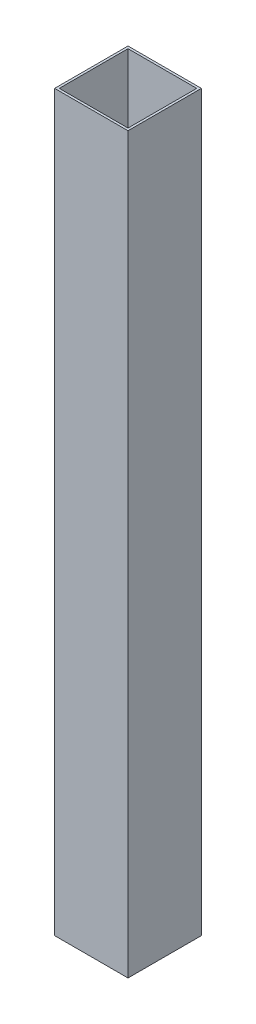
SolidWorks part; units mm, degrees
ref_plane "Front Plane" through (0, 0, 0) normal (0, 0, 1) x (1, 0, 0)
ref_plane "Top Plane" through (0, 0, 0) normal (0, 1, 0) x (1, 0, 0)
ref_plane "Right Plane" through (0, 0, 0) normal (1, 0, 0) x (0, 0, -1)
sketch "Sketch1" plane through (0, 0, 0) normal (0, 1, 0) x (1, 0, 0)
  line L1 (0, 0) -> (50.8, 0)
  line L2 (0, 0) -> (0, 50.8)
  line L3 (0, 50.8) -> (50.8, 50.8)
  line L4 (50.8, 0) -> (50.8, 50.8)
  line L5 (1.6002, 49.1998) -> (49.1998, 49.1998)
  line L6 (1.6002, 49.1998) -> (1.6002, 1.6002)
  line L7 (1.6002, 1.6002) -> (49.1998, 1.6002)
  line L8 (49.1998, 49.1998) -> (49.1998, 1.6002)
  dimension "D1" = 1.6002
  dimension "D2" = 1.6002
  dimension "D3" = 1.6002
  dimension "D4" = 1.6002
  dimension "D5" = 50.8
  dimension "D6" = 50.8
extrude "Boss-Extrude1" add sketch "Sketch1" along normal blind 508
equation "\"3oin\"=0.1"
